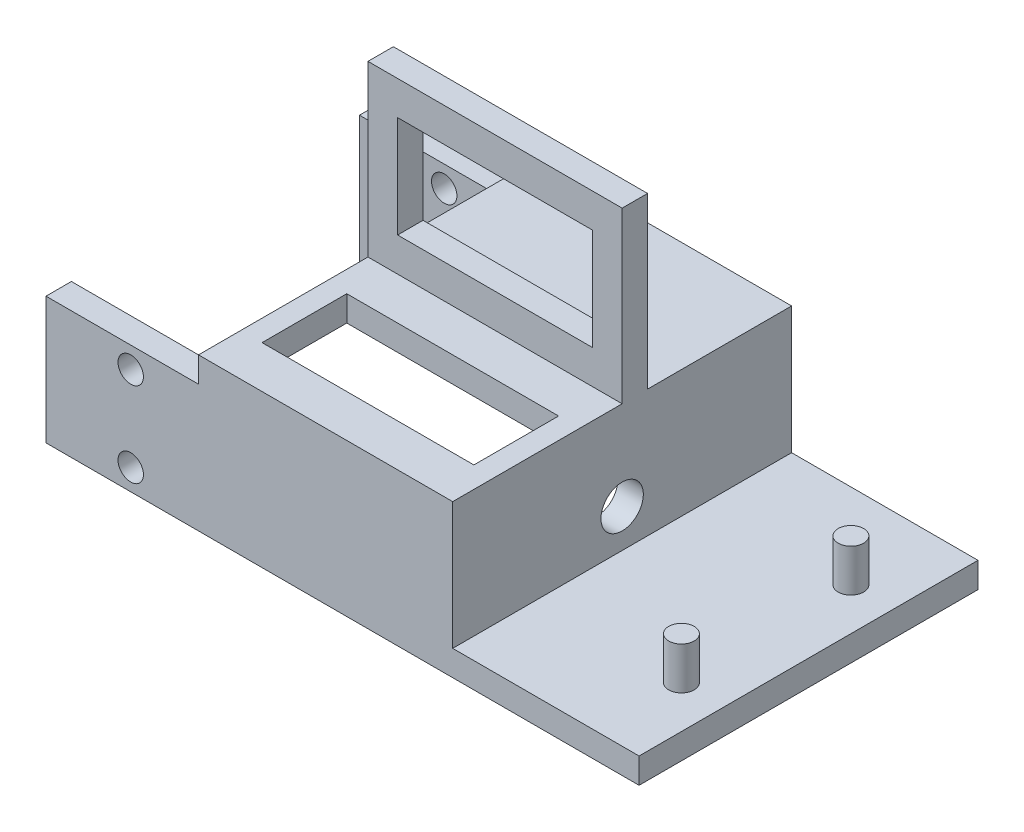
SolidWorks part; units mm, degrees
ref_plane "Front Plane" through (0, 0, 0) normal (0, 0, 1) x (1, 0, 0)
ref_plane "Top Plane" through (0, 0, 0) normal (0, 1, 0) x (1, 0, 0)
ref_plane "Right Plane" through (0, 0, 0) normal (1, 0, 0) x (0, 0, -1)
sketch "Sketch1" plane through (0, 0, 0) normal (0, 0, 1) x (1, 0, 0)
  line L0 (0, 0) -> (25, 0)
  line L1 (25, 0) -> (25, 3)
  line L2 (25, 3) -> (3, 3)
  line L3 (3, 3) -> (3, 15)
  line L4 (3, 15) -> (0, 15)
  line L5 (0, 15) -> (0, 0)
  dimension "D1" = 25
  dimension "D2" = 3
  dimension "D3" = 3
  dimension "D4" = 15
extrude "Boss-Extrude1" add sketch "Sketch1" along normal blind 40
sketch "Sketch2" plane through (0, 3, 0) normal (0, 1, 0) x (1, 0, 0)
  line L0 (3, -20) -> (25, -20) construction
  line L1 (3, -40) -> (3, 0) construction
  line L2 (25, -40) -> (25, 0) construction
  circle A0 centre (20, -10) radius 1.5
  circle A1 centre (20, -30) radius 1.5
  dimension "D1" = 3
  dimension "D2" = 5
  dimension "D3" = 10
extrude "Boss-Extrude2" add sketch "Sketch2" along normal blind 5
sketch "Sketch3" plane through (0, 0, 0) normal (-1, 0, 0) x (0, 0, 1)
  line L0 (20, 15) -> (20, 0) construction
  line L1 (40, 15) -> (0, 15) construction
  line L2 (40, 0) -> (0, 0) construction
  line L3 (0, 7.5) -> (40, 7.5) construction
  line L4 (0, 15) -> (0, 0) construction
  line L5 (40, 15) -> (40, 0) construction
  circle A0 centre (20, 7.5) radius 2.5
  dimension "D1" = 5
extrude "Cut-Extrude1" cut sketch "Sketch3" against normal through all both and the other way through all
sketch "Sketch4" plane through (0, 0, 0) normal (0, 0, -1) x (-1, 0, 0)
  line L0 (0, 15) -> (0, 0) construction
  line L1 (0, 15) -> (45, 15)
  line L2 (0, 15) -> (0, 0)
  line L3 (0, 0) -> (45, 0)
  line L4 (45, 15) -> (45, 0)
  line L5 (0, 0) -> (-25, 0) construction
  line L6 (-3, 15) -> (0, 15) construction
  dimension "D1" = 45
extrude "Boss-Extrude3" add sketch "Sketch4" against normal blind 3
sketch "Sketch5" plane through (0, 0, 40) normal (0, 0, 1) x (1, 0, 0)
  line L1 (0, 15) -> (-45, 15)
  line L2 (0, 15) -> (0, 0)
  line L3 (0, 0) -> (-45, 0)
  line L4 (-45, 15) -> (-45, 0)
extrude "Boss-Extrude4" add sketch "Sketch5" against normal blind 3
sketch "Sketch6" plane through (0, 0, 40) normal (0, 0, 1) x (1, 0, 0)
  line L0 (-45, 7.5) -> (3, 7.5) construction
  line L1 (-45, 15) -> (-45, 0) construction
  line L2 (3, 3) -> (3, 15) construction
  circle A1 centre (-35, 12.5) radius 1.5
  circle A2 centre (-35, 2.5) radius 1.5
  dimension "D2" = 5
  dimension "D3" = 10
  dimension "D1" = 3
extrude "Cut-Extrude2" cut sketch "Sketch6" against normal through all both and the other way through all
sketch "Sketch8" plane through (0, 15, 0) normal (0, 1, 0) x (1, 0, 0)
  line L0 (3, -40) -> (-45, -40) construction
  line L1 (3, -40) -> (-27, -40)
  line L2 (3, -40) -> (3, 0)
  line L3 (3, 0) -> (-27, 0)
  line L4 (-27, -40) -> (-27, 0)
  line L5 (25, -40) -> (3, -40) construction
  line L6 (3, 0) -> (-45, 0) construction
  line L7 (3, -40) -> (3, 0) construction
  line L8 (-12, 0) -> (-12, -40) construction
  line L9 (-24.5, -25) -> (0.5, -25)
  line L10 (-24.5, -25) -> (-24.5, -35)
  line L11 (-24.5, -35) -> (0.5, -35)
  line L12 (0.5, -25) -> (0.5, -35)
  line L13 (-24.5, -25) -> (0.5, -35) construction
  line L14 (-24.5, -35) -> (0.5, -25) construction
  point P13 (-12, -30)
  dimension "D1" = 30
  dimension "D2" = 10
  dimension "D3" = 25
  dimension "D4" = 5
extrude "Boss-Extrude7" add sketch "Sketch8" along normal blind 3
sketch "Sketch9" plane through (0, 18, 0) normal (0, 1, 0) x (1, 0, 0)
  line L0 (-27, -20) -> (3, -20) construction
  line L1 (-27, 0) -> (-27, -40) construction
  line L2 (3, -40) -> (3, 0) construction
  line L3 (3, 0) -> (-27, 0) construction
  dimension "D1" = 20
sketch3d "3DSketch1"
  line L0 (-27, 18, 0) -> (-27, 18, 40) construction
  line L1 (-27, 18, 20) -> (3, 18, 20)
  line L2 (-27, 18, 20) -> (-27, 38, 20)
  line L3 (-27, 38, 20) -> (3, 38, 20)
  line L4 (3, 18, 20) -> (3, 38, 20)
  line L5 (-12, 38, 20) -> (-12, 18, 20) construction
  line L6 (-27, 28, 20) -> (3, 28, 20) construction
  line L8 (-23.5, 34, 20) -> (-0.5, 34, 20)
  line L9 (-23.5, 34, 20) -> (-23.5, 22, 20)
  line L10 (-23.5, 22, 20) -> (-0.5, 22, 20)
  line L11 (-0.5, 34, 20) -> (-0.5, 22, 20)
  line L12 (-23.5, 34, 20) -> (-0.5, 22, 20) construction
  line L13 (-23.5, 22, 20) -> (-0.5, 34, 20) construction
  point P11 (-12, 28, 20)
  dimension "D1" = 20
  dimension "D2" = 23
  dimension "D3" = 12
extrude "Boss-Extrude8" add sketch "3DSketch1" along direction (0, 0, 1) on the side of the normal blind 3 contours L3 L4 L1 L2 | L8 L11 L10 L9
